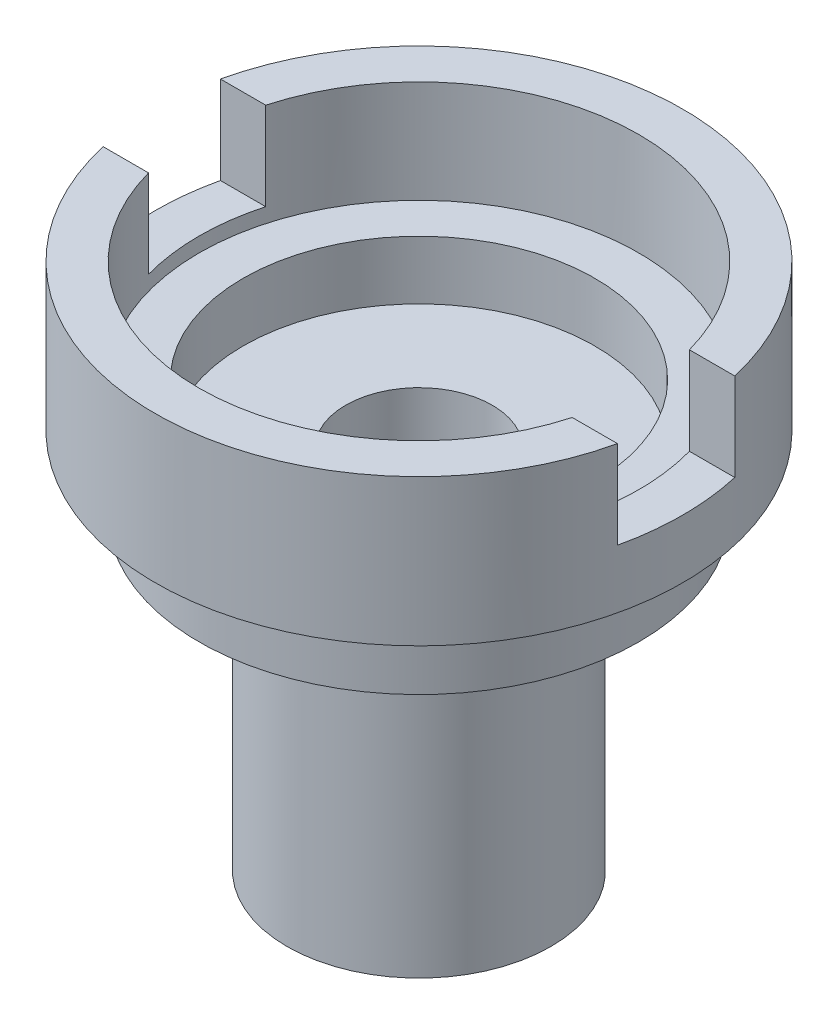
SolidWorks part; units mm, degrees
ref_plane "Front Plane" through (0, 0, 0) normal (0, 0, 1) x (1, 0, 0)
ref_plane "Top Plane" through (0, 0, 0) normal (0, 1, 0) x (1, 0, 0)
ref_plane "Right Plane" through (0, 0, 0) normal (1, 0, 0) x (0, 0, -1)
sketch "Sketch1" plane through (0, 0, 0) normal (0, 0, 1) x (1, 0, 0)
  line L0 (0, 209.3278) -> (0, -40.6722) construction
  line L1 (0, 0) -> (-45, 0)
  line L2 (-45, 0) -> (-45, 105)
  line L3 (-45, 105) -> (-75, 105)
  line L4 (-75, 105) -> (-75, 130)
  line L5 (-75, 130) -> (-90, 130)
  line L6 (-90, 130) -> (-90, 180)
  line L7 (-90, 180) -> (0, 180)
  line L8 (0, 180) -> (0, 0)
  dimension "D1" = 45
  dimension "D2" = 105
  dimension "D3" = 25
  dimension "D4" = 50
  dimension "D5" = 75
  dimension "D6" = 90
revolve "Revolve1" add sketch "Sketch1" angle 360 about L0
sketch "Sketch2" plane through (0, 0, 0) normal (0, 0, 1) x (1, 0, 0)
  line L0 (25, 0) -> (25, 125)
  line L1 (0, 180) -> (0, 0)
  line L2 (0, 180) -> (0, 0) construction
  line L3 (90, 180) -> (-90, 180) construction
  line L4 (0, 0) -> (25, 0)
  line L5 (-45, 0) -> (45, 0) construction
  line L6 (25, 125) -> (60, 125)
  line L8 (60, 145) -> (75, 145)
  line L9 (75, 145) -> (75, 180)
  line L10 (75, 180) -> (0, 180)
  line L11 (60, 145) -> (60, 125)
  dimension "D1" = 25
  dimension "D2" = 125
  dimension "D3" = 20
  dimension "D4" = 35
  dimension "D5" = 75
  dimension "D6" = 60
revolve "Cut-Revolve3" cut sketch "Sketch2" angle 360 about L2
sketch "Sketch3" plane through (0, 180, 0) normal (0, 1, 0) x (1, 0, 0)
  line L1 (-114.8317, 20) -> (114.8317, 20)
  line L2 (-114.8317, 20) -> (-114.8317, -20)
  line L3 (-114.8317, -20) -> (114.8317, -20)
  line L4 (114.8317, 20) -> (114.8317, -20)
  line L5 (-114.8317, 20) -> (114.8317, -20) construction
  line L6 (-114.8317, -20) -> (114.8317, 20) construction
  point P0 (0, 0)
  dimension "D1" = 40
extrude "Cut-Extrude1" cut sketch "Sketch3" against normal blind 30 contours L2 L1 L4 L3
